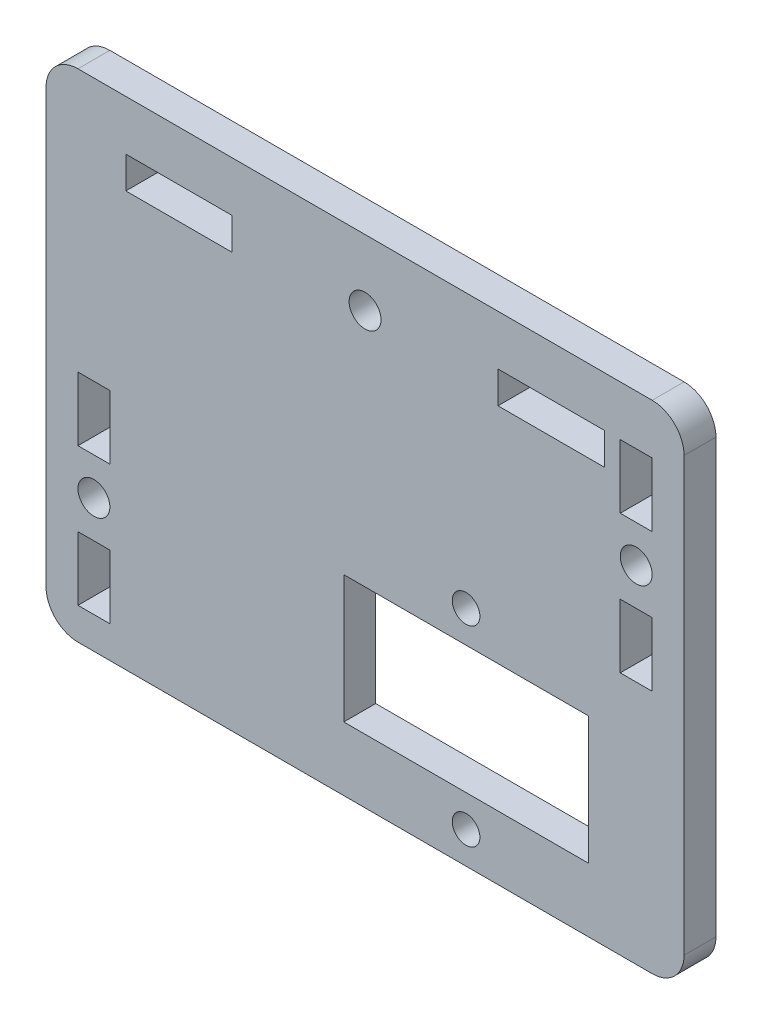
SolidWorks part; units mm, degrees
ref_plane "Front Plane" through (0, 0, 0) normal (0, 0, 1) x (1, 0, 0)
ref_plane "Top Plane" through (0, 0, 0) normal (0, 1, 0) x (1, 0, 0)
ref_plane "Right Plane" through (0, 0, 0) normal (1, 0, 0) x (0, 0, -1)
sketch "Model" plane through (0, 0, 0) normal (0, 0, 1) x (1, 0, 0)
  line L0 (28.4731, 22.668) -> (28.4732, 63.368)
  line L1 (85.4731, 19.668) -> (31.4731, 19.668)
  line L2 (31.4731, 66.368) -> (85.4731, 66.368)
  line L3 (88.4731, 63.3683) -> (88.4731, 22.668)
  line L4 (31.4731, 35.668) -> (34.4731, 35.668)
  line L5 (34.4731, 41.668) -> (31.4731, 41.668)
  line L6 (31.4731, 35.668) -> (31.4731, 41.668)
  line L7 (34.4731, 35.668) -> (34.4731, 41.668)
  line L8 (35.9731, 58.668) -> (35.9731, 61.668)
  line L9 (45.9731, 58.668) -> (45.9731, 61.668)
  line L10 (31.4731, 22.668) -> (34.4731, 22.668)
  line L11 (31.4731, 28.668) -> (34.4731, 28.668)
  line L12 (70.9731, 58.668) -> (70.9731, 61.668)
  line L13 (80.9731, 58.668) -> (80.9731, 61.668)
  line L14 (82.4731, 55.668) -> (82.4731, 61.668)
  line L15 (85.4731, 55.668) -> (85.4731, 61.668)
  line L16 (82.4731, 42.668) -> (82.4731, 48.668)
  line L17 (85.4731, 42.668) -> (85.4731, 48.668)
  line L18 (56.4731, 25.668) -> (56.4731, 37.668)
  line L19 (79.4731, 25.668) -> (79.4731, 37.668)
  line L20 (31.4731, 22.668) -> (31.4731, 28.668)
  line L21 (34.4731, 22.668) -> (34.4731, 28.668)
  line L22 (35.9731, 61.668) -> (45.9731, 61.668)
  line L23 (45.9731, 58.668) -> (35.9731, 58.668)
  line L24 (70.9731, 61.668) -> (80.9731, 61.668)
  line L25 (80.9731, 58.668) -> (70.9731, 58.668)
  line L26 (56.4731, 37.668) -> (79.4731, 37.668)
  line L27 (79.4731, 25.668) -> (56.4731, 25.668)
  line L28 (82.4731, 61.668) -> (85.4731, 61.668)
  line L29 (82.4731, 55.668) -> (85.4731, 55.668)
  line L30 (85.4731, 48.668) -> (82.4731, 48.668)
  line L31 (82.4731, 42.668) -> (85.4731, 42.668)
  arc A0 (28.4731, 22.668) -> (31.4731, 19.668) centre (31.473, 22.6679) ccw
  circle A1 centre (32.9731, 32.168) radius 1.5
  circle A2 centre (58.4731, 60.168) radius 1.5
  circle A3 centre (67.9731, 22.668) radius 1.3
  circle A4 centre (67.9731, 40.668) radius 1.3
  circle A5 centre (83.9731, 52.168) radius 1.5
  arc A6 (31.4731, 66.368) -> (28.4732, 63.368) centre (31.4731, 63.368) ccw
  arc A7 (88.4731, 63.3683) -> (85.4731, 66.368) centre (85.4733, 63.3683) ccw
  arc A8 (85.4731, 19.668) -> (88.4731, 22.668) centre (85.4735, 22.6676) ccw
extrude "Boss-Extrude1" add sketch "Model" along normal blind 3
